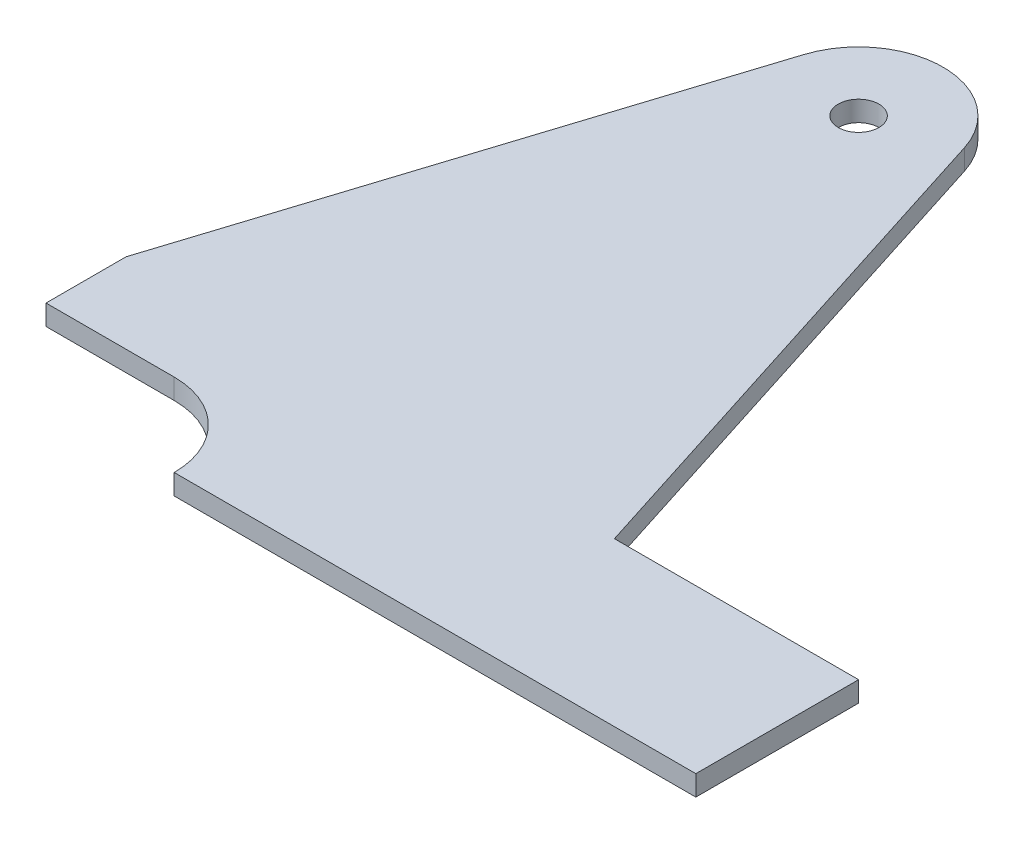
SolidWorks part; units mm, degrees
ref_plane "Front Plane" through (0, 0, 0) normal (0, 0, 1) x (1, 0, 0)
ref_plane "Top Plane" through (0, 0, 0) normal (0, 1, 0) x (1, 0, 0)
ref_plane "Right Plane" through (0, 0, 0) normal (1, 0, 0) x (0, 0, -1)
sketch "Sketch1" plane through (0, 0, 0) normal (0, 1, 0) x (1, 0, 0)
  line L1 (76.2, -152.4) -> (25.107, 7.9976)
  line L2 (-76.2, -152.4) -> (-25.107, 7.9976)
  line L3 (0, 67.2626) -> (0, -107.7613) construction
  line L4 (76.2, -152.4) -> (152.4, -152.4)
  line L5 (152.4, -152.4) -> (152.4, -203.2)
  line L8 (-76.2, -152.4) -> (76.2, -152.4) construction
  line L10 (152.4, -203.2) -> (-10.4, -203.2)
  line L12 (-76.2, -152.4) -> (-76.2, -177.4)
  line L13 (-76.2, -177.4) -> (-36.2, -177.4)
  circle A0 centre (0, 0) radius 6.35
  arc A1 (-25.107, 7.9976) -> (25.107, 7.9976) centre (0, 0) cw
  arc A3 (-10.4, -203.2) -> (-36.2, -177.4) centre (-36.2, -203.2) ccw
  point P12 (0, -152.4)
  point P16 (0, 0)
  point P17 (0, 0)
  point P18 (0, 0)
  point P19 (0, 0)
  point P20 (0, 0)
  point P21 (0, 0)
  dimension "D3" = 20
  dimension "D4" = 12.7
  dimension "D1" = 228.6
  dimension "D2" = 152.4
  dimension "D5" = 152.4
  dimension "D6" = 40
  dimension "D7" = 50.8
  dimension "D8" = 25
extrude "Boss-Extrude1" add sketch "Sketch1" along normal blind 6.35
